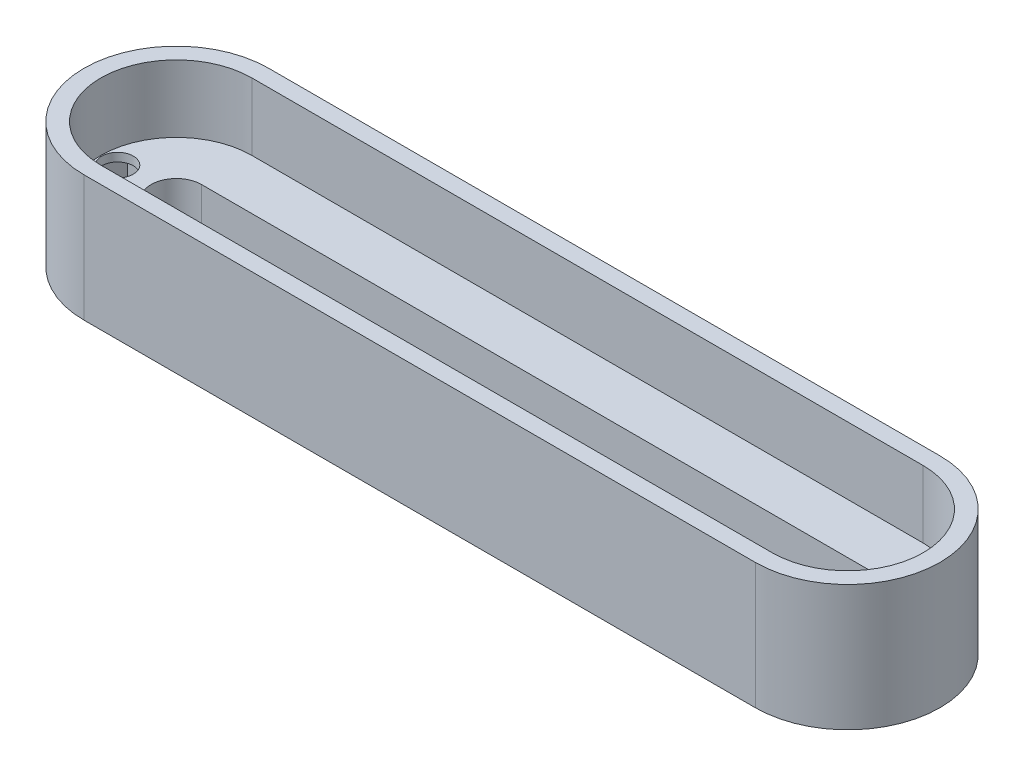
SolidWorks part; units mm, degrees
ref_plane "Front" through (0, 0, 0) normal (0, 0, 1) x (1, 0, 0)
ref_plane "Top" through (0, 0, 0) normal (0, 1, 0) x (1, 0, 0)
ref_plane "Right" through (0, 0, 0) normal (1, 0, 0) x (0, 0, -1)
sketch "Croquis1" plane through (0, 0, 0) normal (0, 1, 0) x (1, 0, 0)
  line L0 (-40, 0) -> (40, 0) construction
  line L1 (-40, 3) -> (40, 3)
  line L2 (-40, -3) -> (40, -3)
  line L3 (-40, 0) -> (40, 0) construction
  line L4 (-40, 11) -> (40, 11)
  line L5 (-40, -11) -> (40, -11)
  arc A0 (-40, 3) -> (-40, -3) centre (-40, 0) ccw
  arc A1 (40, -3) -> (40, 3) centre (40, 0) ccw
  arc A2 (-40, 11) -> (-40, -11) centre (-40, 0) ccw
  arc A3 (40, -11) -> (40, 11) centre (40, 0) ccw
  point P3 (0, 0)
  point P8 (0, 0)
  dimension "D2" = 3
  dimension "D1" = 80
  dimension "D3" = 8
extrude "Saliente-Extruir1" add sketch "Croquis1" along normal blind 12
sketch "Croquis2" plane through (0, 0, 0) normal (0, 1, 0) x (1, 0, 0)
  line L0 (-47, 0) -> (47, 0) construction
  line L2 (-45.4, -2.7713) -> (-43.8, 0)
  line L3 (-43.8, 0) -> (-45.4, 2.7713)
  line L4 (-45.4, 2.7713) -> (-48.6, 2.7713)
  line L5 (-48.6, 2.7713) -> (-50.2, 0)
  line L6 (-50.2, 0) -> (-48.6, -2.7713)
  line L7 (-48.6, -2.7713) -> (-45.4, -2.7713)
  line L9 (0, 0) -> (0, -3) construction
  line L10 (51, 0) -> (43, 0) construction
  line L12 (48.6, -2.7713) -> (45.4, -2.7713)
  line L13 (-51, 0) -> (-43, 0) construction
  line L14 (50.2, 0) -> (48.6, -2.7713)
  line L15 (48.6, 2.7713) -> (50.2, 0)
  line L16 (-40, -11) -> (40, -11)
  line L17 (40, 11) -> (-40, 11)
  line L18 (-40, -11) -> (40, -11)
  line L19 (40, 11) -> (-40, 11)
  line L20 (45.4, 2.7713) -> (48.6, 2.7713)
  line L21 (43.8, 0) -> (45.4, 2.7713)
  line L22 (-40, -3) -> (40, -3)
  line L23 (40, 3) -> (-40, 3)
  line L24 (-40, -3) -> (40, -3)
  line L25 (40, 3) -> (-40, 3)
  line L26 (45.4, -2.7713) -> (43.8, 0)
  circle A0 centre (-47, 0) radius 2.7713 construction
  circle A1 centre (47, 0) radius 2.7713 construction
  arc A2 (-40, 11) -> (-40, -11) centre (-40, 0) ccw construction
  arc A3 (-40, 3) -> (-40, -3) centre (-40, 0) ccw construction
  arc A6 (-40, 11) -> (-40, -11) centre (-40, 0) ccw
  arc A7 (40, -11) -> (40, 11) centre (40, 0) ccw
  arc A8 (-40, 11) -> (-40, -11) centre (-40, 0) ccw
  arc A9 (40, -11) -> (40, 11) centre (40, 0) ccw
  arc A12 (-40, 3) -> (-40, -3) centre (-40, 0) ccw
  arc A13 (40, -3) -> (40, 3) centre (40, 0) ccw
  arc A14 (-40, 3) -> (-40, -3) centre (-40, 0) ccw
  arc A15 (40, -3) -> (40, 3) centre (40, 0) ccw
  point P9 (0, 0)
  point P17 (-47, 0)
  dimension "D1" = 3.2
  dimension "D2" = 0
  dimension "D3" = 0
extrude "Cortar-Extruir1" cut sketch "Croquis2" along normal blind 6 contours L26 L12 L14 L15 L20 L21 | L4 L5 L6 L7 L2 L3
sketch "Croquis5" plane through (0, 6, 0) normal (0, -1, 0) x (1, 0, 0)
  line L0 (-48.6, 2.7713) -> (-45.4, -2.7713) construction
  line L1 (0, 0) -> (0, -4.4647) construction
  line L2 (40, 3) -> (-40, 3)
  line L3 (-40, -3) -> (40, -3)
  line L4 (40, 3) -> (-40, 3)
  line L5 (-40, -3) -> (40, -3)
  line L6 (-43.8, 0) -> (-45.4, 2.7713)
  line L7 (-45.4, -2.7713) -> (-43.8, 0)
  line L8 (-48.6, -2.7713) -> (-45.4, -2.7713)
  line L9 (-50.2, 0) -> (-48.6, -2.7713)
  line L10 (-48.6, 2.7713) -> (-50.2, 0)
  line L11 (-45.4, 2.7713) -> (-48.6, 2.7713)
  line L12 (-43.8, 0) -> (-45.4, 2.7713)
  line L13 (-45.4, -2.7713) -> (-43.8, 0)
  line L14 (-48.6, -2.7713) -> (-45.4, -2.7713)
  line L15 (-50.2, 0) -> (-48.6, -2.7713)
  line L16 (-48.6, 2.7713) -> (-50.2, 0)
  line L17 (-45.4, 2.7713) -> (-48.6, 2.7713)
  line L18 (40, 11) -> (-40, 11)
  line L19 (-40, -11) -> (40, -11)
  line L20 (40, 11) -> (-40, 11)
  line L21 (-40, -11) -> (40, -11)
  line L26 (48.6, 2.7713) -> (45.4, 2.7713)
  line L27 (50.2, 0) -> (48.6, 2.7713)
  line L28 (48.6, -2.7713) -> (50.2, 0)
  line L29 (45.4, -2.7713) -> (48.6, -2.7713)
  line L30 (43.8, 0) -> (45.4, -2.7713)
  line L31 (45.4, 2.7713) -> (43.8, 0)
  line L32 (48.6, 2.7713) -> (45.4, 2.7713)
  line L33 (50.2, 0) -> (48.6, 2.7713)
  line L34 (48.6, -2.7713) -> (50.2, 0)
  line L35 (45.4, -2.7713) -> (48.6, -2.7713)
  line L36 (43.8, 0) -> (45.4, -2.7713)
  line L37 (45.4, 2.7713) -> (43.8, 0)
  circle A0 centre (-47, 0) radius 1.875
  circle A1 centre (47, 0) radius 1.875
  arc A2 (40, -3) -> (40, 3) centre (40, 0) ccw
  arc A3 (-40, 3) -> (-40, -3) centre (-40, 0) ccw
  arc A4 (40, -3) -> (40, 3) centre (40, 0) ccw
  arc A5 (-40, 3) -> (-40, -3) centre (-40, 0) ccw
  arc A6 (40, -11) -> (40, 11) centre (40, 0) ccw
  arc A7 (-40, 11) -> (-40, -11) centre (-40, 0) ccw
  arc A8 (40, -11) -> (40, 11) centre (40, 0) ccw
  arc A9 (-40, 11) -> (-40, -11) centre (-40, 0) ccw
  dimension "D5" = 3.75
  dimension "D1" = 0
  dimension "D2" = 0
  dimension "D3" = 0
  dimension "D4" = 0
extrude "Cortar-Extruir2" cut sketch "Croquis5" against normal through all both and the other way through all contours A0 | A1
sketch "Croquis6" plane through (0, 12, 0) normal (0, 1, 0) x (1, 0, 0)
  line L0 (-40, 11) -> (-40, -11)
  line L1 (40, 11) -> (40, -11)
  line L2 (-40, -11) -> (40, -11)
  line L3 (40, 11) -> (-40, 11)
  line L4 (-40, -11) -> (40, -11)
  line L5 (40, 11) -> (-40, 11)
  line L10 (-40, -3) -> (40, -3)
  line L11 (40, 3) -> (-40, 3)
  line L12 (-40, -3) -> (40, -3)
  line L13 (40, 3) -> (-40, 3)
  arc A2 (-40, 11) -> (-40, -11) centre (-40, 0) ccw
  arc A3 (40, -11) -> (40, 11) centre (40, 0) ccw
  arc A4 (-40, 11) -> (-40, -11) centre (-40, 0) ccw
  arc A5 (40, -11) -> (40, 11) centre (40, 0) ccw
  circle A9 centre (-47, 0) radius 1.875
  arc A10 (-40, 3) -> (-40, -3) centre (-40, 0) ccw
  arc A11 (40, -3) -> (40, 3) centre (40, 0) ccw
  arc A12 (-40, 3) -> (-40, -3) centre (-40, 0) ccw
  arc A13 (40, -3) -> (40, 3) centre (40, 0) ccw
  circle A14 centre (-47, 0) radius 1.875
  circle A15 centre (47, 0) radius 1.875
  circle A16 centre (47, 0) radius 1.875
  circle M11 centre (47, 0) radius 1.875
  circle M12 centre (-47, 0) radius 1.875
  arc M13 (-40, 11) -> (-40, -11) centre (-40, 0) ccw
  line M14 (-40, -11) -> (40, -11)
  arc M15 (40, -11) -> (40, 11) centre (40, 0) ccw
  line M16 (40, 11) -> (-40, 11)
  line M17 (40, -3) -> (-40, -3)
  arc M18 (-40, -3) -> (-40, 3) centre (-40, 0) cw
  line M19 (-40, 3) -> (40, 3)
  arc M20 (40, 3) -> (40, -3) centre (40, 0) cw
  dimension "D2" = 0
  dimension "D1" = 0
  dimension "D3" = 0
  dimension "D4" = 0
extrude "Saliente-Extruir4" add sketch "Croquis6" along normal blind 3 contours L1 L0 M16 M19 | L1 L0 M17 M14 | L0 M13 M18 M12 | L1 M15 M20 M11
sketch "Croquis7" plane through (0, 15, 0) normal (0, 1, 0) x (1, 0, 0)
  line L0 (-40, 0) -> (40, 0) construction
  line L1 (-40, 9) -> (40, 9)
  line L2 (-40, -9) -> (40, -9)
  arc A0 (-40, 9) -> (-40, -9) centre (-40, 0) ccw
  arc A1 (40, -9) -> (40, 9) centre (40, 0) ccw
  point P4 (0, 0)
  dimension "D1" = 9
extrude "Cortar-Extruir3" cut sketch "Croquis7" against normal blind 8
